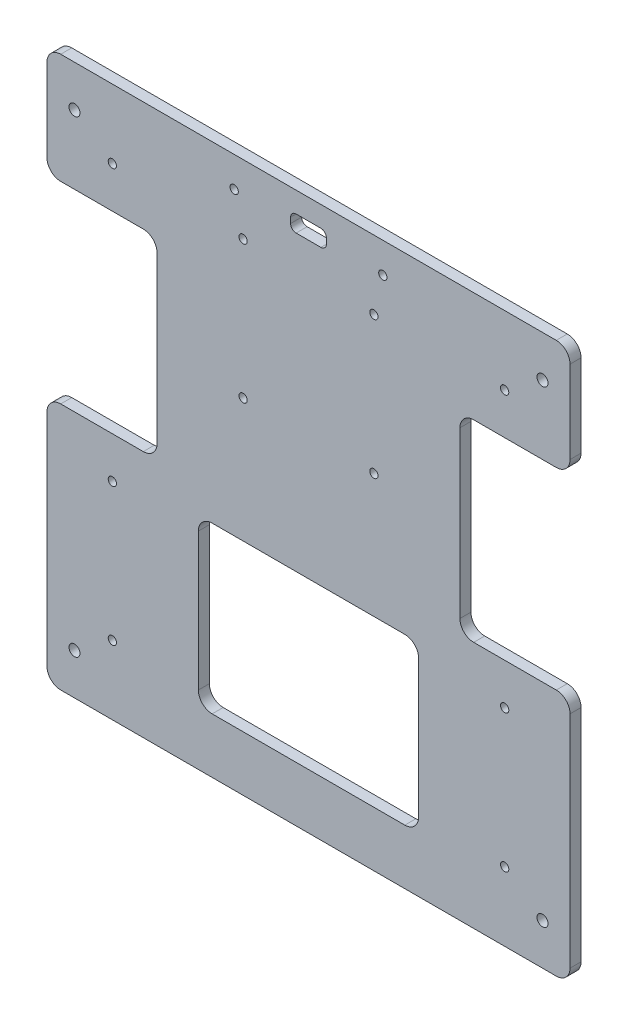
SolidWorks part; units mm, degrees
ref_plane "Front" through (0, 0, 0) normal (0, 0, 1) x (1, 0, 0)
ref_plane "Top" through (0, 0, 0) normal (0, 1, 0) x (1, 0, 0)
ref_plane "Right" through (0, 0, 0) normal (1, 0, 0) x (0, 0, -1)
sketch "Sketch1" plane through (0, 0, 0) normal (0, 0, 1) x (1, 0, 0)
  line L0 (-95, -115) -> (-95, -195)
  line L1 (-90, 0) -> (90, 0)
  line L2 (-95, -5) -> (-95, -35)
  line L3 (-90, -200) -> (90, -200)
  line L4 (95, -5) -> (95, -35)
  line L5 (-90, -40) -> (-60, -40)
  line L7 (-90, -110) -> (-60, -110)
  line L8 (-55, -45) -> (-55, -105)
  line L9 (90, -40) -> (60, -40)
  line L11 (90, -110) -> (60, -110)
  line L12 (55, -45) -> (55, -105)
  line L13 (95, -115) -> (95, -195)
  arc A0 (90, -200) -> (95, -195) centre (90, -195) ccw
  arc A1 (-95, -195) -> (-90, -200) centre (-90, -195) ccw
  arc A2 (90, 0) -> (95, -5) centre (90, -5) cw
  arc A3 (-90, 0) -> (-95, -5) centre (-90, -5) ccw
  arc A4 (90, -40) -> (95, -35) centre (90, -35) ccw
  arc A5 (-90, -40) -> (-95, -35) centre (-90, -35) cw
  arc A6 (-60, -40) -> (-55, -45) centre (-60, -45) cw
  arc A7 (-60, -110) -> (-55, -105) centre (-60, -105) ccw
  arc A8 (-95, -115) -> (-90, -110) centre (-90, -115) cw
  arc A9 (95, -115) -> (90, -110) centre (90, -115) ccw
  arc A10 (60, -110) -> (55, -105) centre (60, -105) cw
  arc A11 (60, -40) -> (55, -45) centre (60, -45) ccw
  point P4 (0, 0)
  point P8 (95, -200)
  point P13 (95, 0)
  point P16 (-95, 0)
  point P27 (95, -40)
  point P30 (-95, -40)
  point P33 (-55, -40)
  point P36 (-55, -110)
  point P43 (55, -110)
  point P46 (55, -40)
  dimension "D3" = 5
  dimension "D10" = 5
  dimension "D11" = 5
  dimension "D1" = 190
  dimension "D2" = 200
  dimension "D4" = 40
  dimension "D5" = 40
  dimension "D6" = 40
  dimension "D7" = 40
  dimension "D8" = 70
  dimension "D9" = 70
extrude "Boss-Extrude1" add sketch "Sketch1" along normal blind 4
sketch "Sketch2" plane through (0, 0, 4) normal (0, 0, 1) x (1, 0, 0)
  line L0 (-90, -200) -> (90, -200) construction
  line L1 (-35, -120) -> (35, -120)
  line L2 (-40, -125) -> (-40, -175)
  line L3 (-35, -180) -> (35, -180)
  line L4 (40, -125) -> (40, -175)
  arc A0 (-40, -175) -> (-35, -180) centre (-35, -175) ccw
  arc A1 (35, -180) -> (40, -175) centre (35, -175) ccw
  arc A2 (35, -120) -> (40, -125) centre (35, -125) cw
  arc A3 (-35, -120) -> (-40, -125) centre (-35, -125) ccw
  point P4 (0, -120)
  dimension "D4" = 5
  dimension "D1" = 60
  dimension "D2" = 80
  dimension "D3" = 20
extrude "Cut-Extrude1" cut sketch "Sketch2" against normal blind 4
sketch "Sketch3" plane through (0, 0, 4) normal (0, 0, 1) x (1, 0, 0)
  line L0 (-90, -200) -> (90, -200) construction
  line L1 (-95, -5) -> (-95, -35) construction
  line L2 (-95, -5) -> (-95, -35) construction
  line L4 (90, 0) -> (-90, 0) construction
  line L5 (0, 62.7511) -> (0, -214.7248) construction
  line L6 (90, 0) -> (-90, 0) construction
  line L7 (-4.5, -7.5) -> (4.5, -7.5)
  line L8 (-6.5, -9.5) -> (-6.5, -11.5)
  line L9 (-4.5, -13.5) -> (4.5, -13.5)
  line L10 (6.5, -9.5) -> (6.5, -11.5)
  circle A0 centre (-85, -15) radius 2
  circle A1 centre (-85, -185) radius 2
  circle A2 centre (85, -185) radius 2
  circle A3 centre (85, -15) radius 2
  arc A4 (-4.5, -7.5) -> (-6.5, -9.5) centre (-4.5, -9.5) ccw
  arc A5 (-6.5, -11.5) -> (-4.5, -13.5) centre (-4.5, -11.5) ccw
  arc A6 (4.5, -13.5) -> (6.5, -11.5) centre (4.5, -11.5) ccw
  arc A7 (4.5, -7.5) -> (6.5, -9.5) centre (4.5, -9.5) cw
  circle A8 centre (-27, -11) radius 1.5
  circle A9 centre (27, -11) radius 1.5
  point P23 (0, -7.5)
  dimension "D1" = 4
  dimension "D2" = 4
  dimension "D8" = 2
  dimension "D9" = 2
  dimension "D10" = 2
  dimension "D11" = 2
  dimension "D14" = 3
  dimension "D15" = 11
  dimension "D16" = 27
  dimension "D3" = 15
  dimension "D4" = 10
  dimension "D5" = 10
  dimension "D6" = 15
  dimension "D7" = 7.5
  dimension "D12" = 9
  dimension "D13" = 2
extrude "Cut-Extrude2" cut sketch "Sketch3" against normal blind 10
sketch "Sketch4" plane through (0, 0, 4) normal (0, 0, 1) x (1, 0, 0)
  line L0 (0, 26.9748) -> (0, -212.2227) construction
  line L1 (115.8199, -50) -> (-126.0891, -50) construction
  line L2 (-122.6021, -100) -> (129.1978, -100) construction
  line L5 (90, 0) -> (-90, 0) construction
  line L6 (-47.5, 19.0058) -> (-47.5, -248.1475) construction
  line L8 (-95, -5) -> (-95, -35) construction
  circle A13 centre (-71.25, -25) radius 1.5
  circle A43 centre (-71.25, -75) radius 1.5
  circle A44 centre (-71.25, -175) radius 1.5
  circle A45 centre (-71.25, -125) radius 1.5
  circle A46 centre (-23.75, -125) radius 1.5
  circle A47 centre (-23.75, -175) radius 1.5
  circle A48 centre (-23.75, -75) radius 1.5
  circle A49 centre (-23.75, -25) radius 1.5
  circle A50 centre (23.75, -25) radius 1.5
  circle A51 centre (23.75, -75) radius 1.5
  circle A52 centre (23.75, -175) radius 1.5
  circle A53 centre (23.75, -125) radius 1.5
  circle A54 centre (71.25, -125) radius 1.5
  circle A55 centre (71.25, -175) radius 1.5
  circle A56 centre (71.25, -75) radius 1.5
  circle A57 centre (71.25, -25) radius 1.5
  dimension "D1" = 50
  dimension "D2" = 100
  dimension "D5" = 95
  dimension "D4" = 47.5
  dimension "D7" = 23.75
  dimension "D8" = 25
extrude "Cut-Extrude3" cut sketch "Sketch4" against normal blind 10
